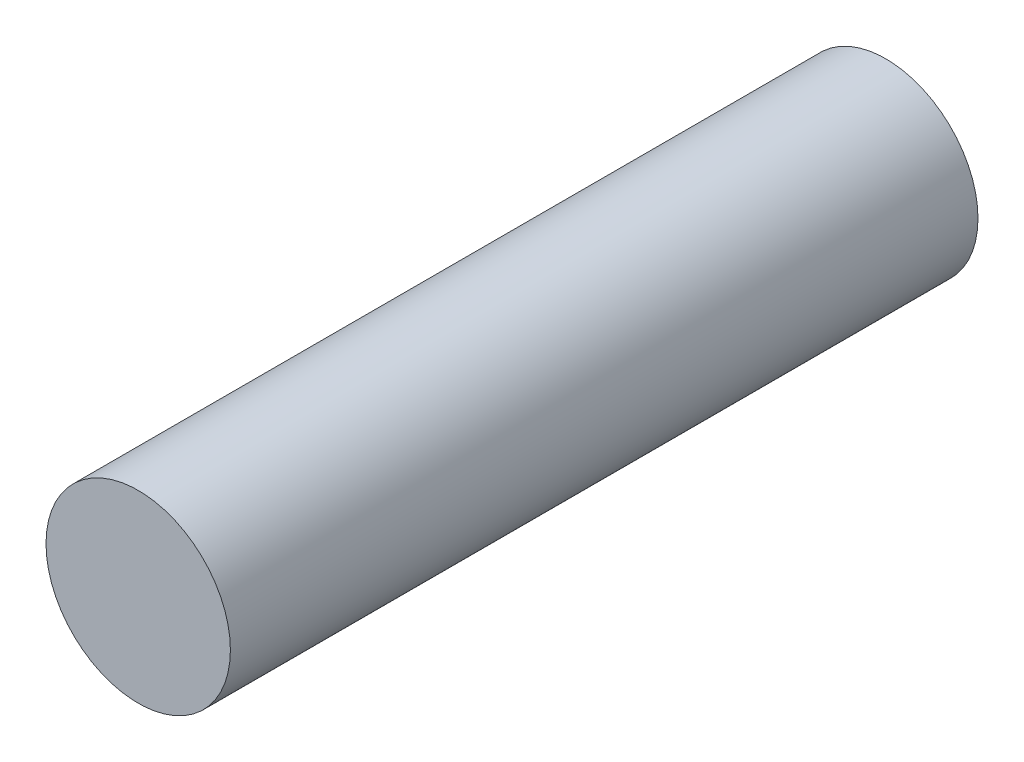
SolidWorks part; units mm, degrees
ref_plane "Front" through (0, 0, 0) normal (0, 0, 1) x (1, 0, 0)
ref_plane "Top" through (0, 0, 0) normal (0, 1, 0) x (1, 0, 0)
ref_plane "Right" through (0, 0, 0) normal (1, 0, 0) x (0, 0, -1)
sketch "Sketch1" plane through (0, 0, 0) normal (0, 0, 1) x (1, 0, 0)
  circle A0 centre (0, 0) radius 4.699
  dimension "D1" = 9.398
extrude "Base-Extrude" add sketch "Sketch1" along normal blind 38.1
scale "Scale1" scale about centroid uniform scaling yes scale factor 0.8
